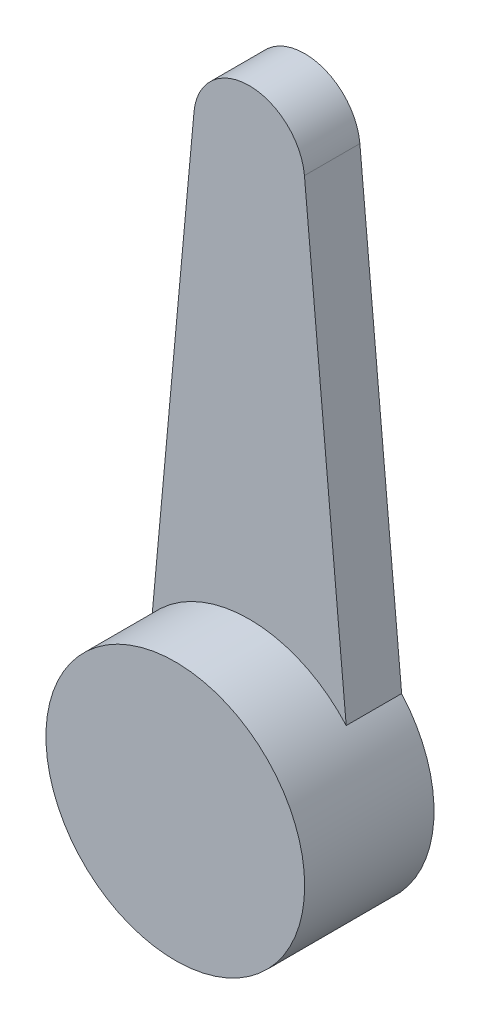
SolidWorks part; units mm, degrees
ref_plane "Front Plane" through (0, 0, 0) normal (0, 0, 1) x (1, 0, 0)
ref_plane "Top Plane" through (0, 0, 0) normal (0, 1, 0) x (1, 0, 0)
ref_plane "Right Plane" through (0, 0, 0) normal (1, 0, 0) x (0, 0, -1)
sketch "Sketch1" plane through (0, 0, 0) normal (0, 0, 1) x (1, 0, 0)
  line L0 (-10.8886, 0) -> (14.367, 0) construction
  line L1 (-10.8886, 16) -> (14.8416, 16) construction
  line L2 (-14.2447, -3.5) -> (29.0796, -3.5) construction
  line L3 (0, 0) -> (0, 18.5714) construction
  line L4 (-1.4937, 14.637) -> (-2.6237, 2.3166)
  line L5 (1.4937, 14.637) -> (2.6237, 2.3166)
  circle A0 centre (0, 0) radius 3.5
  circle A1 centre (0, 14.5) radius 1.5
  point P16 (0, 0)
  point P17 (0, 0)
  point P18 (0, 0)
  point P19 (-2.8857, 1.9806)
  point P20 (3.1056, 1.6142)
  point P21 (2.8716, 1.9806)
  point P22 (0, 0)
  point P23 (3.2028, 1.4114)
  point P24 (-2.0833, 14.8819)
  point P25 (2.5, 13.5)
  point P26 (2.0182, 14.9755)
  point P27 (-2.6237, 2.3166)
  point P28 (0, 0)
  dimension "D1" = 7
  dimension "D3" = 3
  dimension "D2" = 19.5
extrude "Boss-Extrude1" add sketch "Sketch1" along normal blind 1.5 contours A1 L4 A0 L5 | A1
sketch "Sketch2" plane through (0, 0, 1.5) normal (0, 0, 1) x (1, 0, 0)
  circle A0 centre (0, 0) radius 3.5
  arc A1 (-2.6237, 2.3166) -> (2.6237, 2.3166) centre (0, 0) ccw construction
extrude "Boss-Extrude2" add sketch "Sketch2" along normal blind 2
